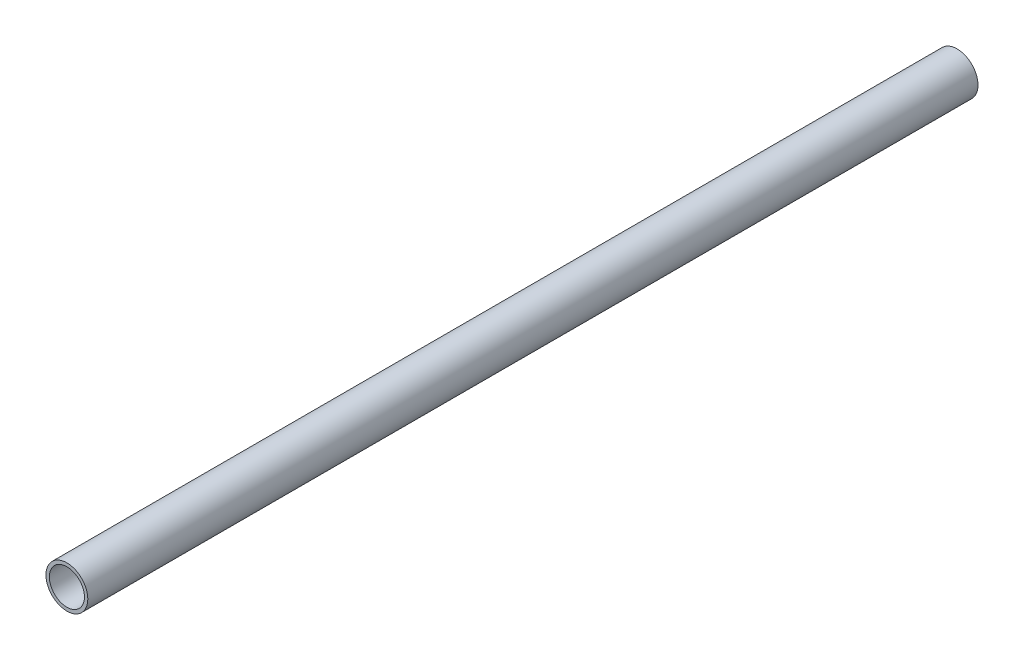
SolidWorks part; units mm, degrees
material "carbon"
ref_plane "Płaszczyzna XY" through (0, 0, 0) normal (0, 0, 1) x (1, 0, 0)
ref_plane "Płaszczyzna XZ" through (0, 0, 0) normal (0, 1, 0) x (1, 0, 0)
ref_plane "Płaszczyzna YZ" through (0, 0, 0) normal (1, 0, 0) x (0, 0, -1)
sketch "Szkic1" plane through (0, 0, 0) normal (0, 0, 1) x (1, 0, 0)
  circle A0 centre (0, 0) radius 7
  circle A1 centre (0, 0) radius 8.35
  dimension "D1" = 14
  dimension "D2" = 16.7
extrude "Dodanie-wyciągnięcie1" add sketch "Szkic1" along normal blind 16.7 and the other way up to surface (338.5197 mm away)
